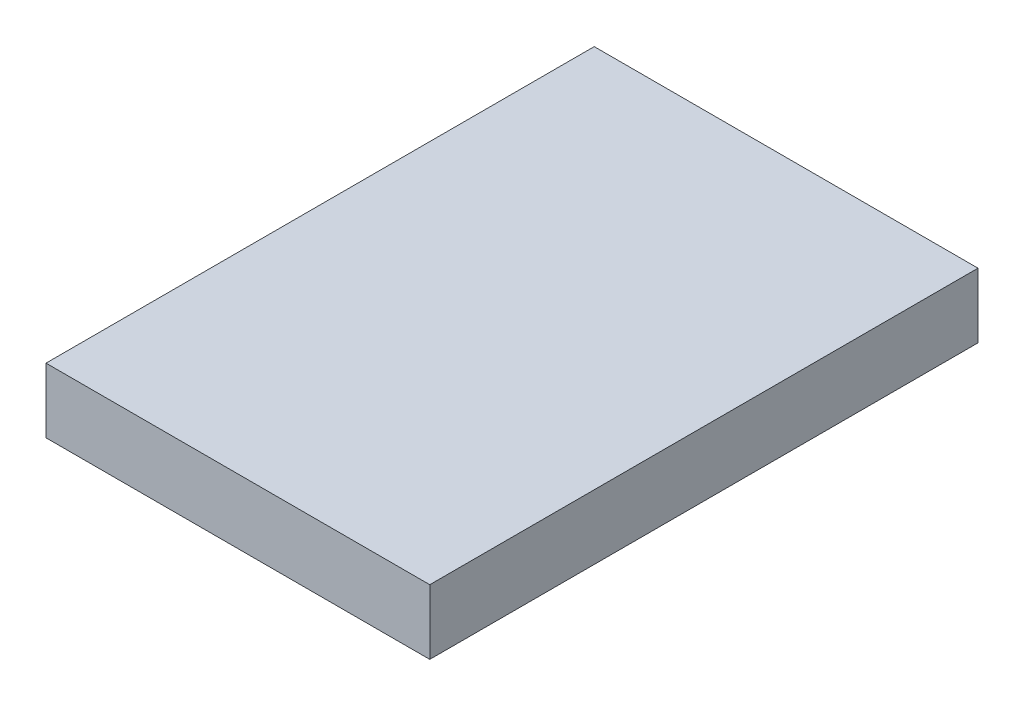
SolidWorks part; units mm, degrees
ref_plane "Front Plane" through (0, 0, 0) normal (0, 0, 1) x (1, 0, 0)
ref_plane "Top Plane" through (0, 0, 0) normal (0, 1, 0) x (1, 0, 0)
ref_plane "Right Plane" through (0, 0, 0) normal (1, 0, 0) x (0, 0, -1)
sketch "Sketch1" plane through (0, 0, 0) normal (0, 1, 0) x (1, 0, 0)
  line L1 (-7, 10) -> (7, 10)
  line L2 (-7, 10) -> (-7, -10)
  line L3 (-7, -10) -> (7, -10)
  line L4 (7, 10) -> (7, -10)
  line L5 (-7, 10) -> (7, -10) construction
  line L6 (-7, -10) -> (7, 10) construction
  point P0 (0, 0)
  dimension "D1" = 20
  dimension "D2" = 14
extrude "Boss-Extrude1" add sketch "Sketch1" along normal blind 2.36
